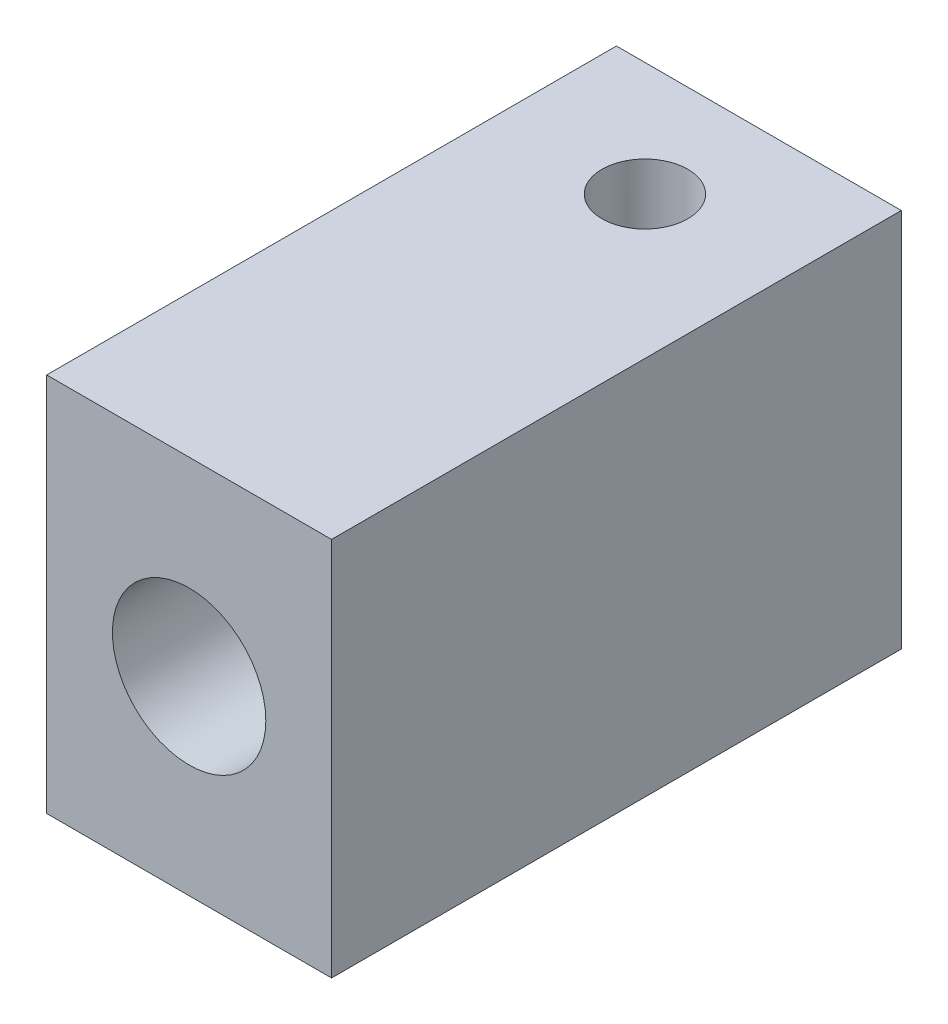
SolidWorks part; units mm, degrees
ref_plane "Front Plane" through (0, 0, 0) normal (0, 0, 1) x (1, 0, 0)
ref_plane "Top Plane" through (0, 0, 0) normal (0, 1, 0) x (1, 0, 0)
ref_plane "Right Plane" through (0, 0, 0) normal (1, 0, 0) x (0, 0, -1)
sketch "Sketch1" plane through (0, 0, 0) normal (0, 0, 1) x (1, 0, 0)
  line L1 (-8.413, 7.2391) -> (-0.913, 7.2391)
  line L2 (-8.413, 7.2391) -> (-8.413, -2.7609)
  line L3 (-8.413, -2.7609) -> (-0.913, -2.7609)
  line L4 (-0.913, 7.2391) -> (-0.913, -2.7609)
  dimension "D1" = 10
extrude "Boss-Extrude1" add sketch "Sketch1" along normal blind 15
sketch "10-32 hole for luer screw" plane through (0, 0, 15) normal (0, 0, 1) x (1, 0, 0)
  line L0 (-8.413, 7.2391) -> (-0.913, -2.7609) construction
  circle A0 centre (-4.663, 2.2391) radius 2.0193
  point P4 (-4.663, 2.2391)
  dimension "D1" = 4.0386
sketch "hole for tubing" plane through (0, 0, 0) normal (0, 0, -1) x (-1, 0, 0)
  line L0 (0.913, 7.2391) -> (8.413, -2.7609) construction
  circle A0 centre (4.663, 2.2391) radius 1.1
  point P4 (4.663, 2.2391)
  dimension "D1" = 2.2
extrude "Cut-Extrude1" cut sketch "hole for tubing" against normal through all
extrude "Cut-Extrude2" cut sketch "10-32 hole for luer screw" against normal blind 7.5
sketch "4-40 set screw hole" plane through (0, 7.2391, 0) normal (0, 1, 0) x (1, 0, 0)
  line L0 (-0.913, 0) -> (-8.413, -6) construction
  line L1 (-8.413, -15) -> (-8.413, 0) construction
  circle A0 centre (-4.663, -3) radius 1.1303
  dimension "D2" = 2.2606
  dimension "D1" = 6
extrude "Cut-Extrude3" cut sketch "4-40 set screw hole" against normal through all
sketch "Sketch2" plane through (0, 0, 0) normal (0, 0, -1) x (-1, 0, 0)
  line L0 (0.913, -2.7609) -> (8.413, 4.7391) construction
  line L1 (2.7185, -0.9554) -> (6.6076, -0.9554)
  line L2 (2.7185, -0.9554) -> (2.7185, 2.9337)
  line L3 (2.7185, 2.9337) -> (6.6076, 2.9337)
  line L4 (6.6076, -0.9554) -> (6.6076, 2.9337)
  line L5 (6.6076, -0.9554) -> (2.7185, 2.9337) construction
  line L7 (0, -3.9595) -> (7.0377, -3.9595)
  line L8 (0, -3.9595) -> (0, 4.2272)
  line L9 (0, 4.2272) -> (7.0377, 4.2272)
  line L10 (7.0377, -3.9595) -> (7.0377, 4.2272)
  point P8 (4.663, 0.9891)
  point P9 (4.663, 0.9891)
  dimension "D1" = 5.5
extrude "Cut-Extrude4" [suppressed] cut sketch "Sketch2" against normal blind 5
